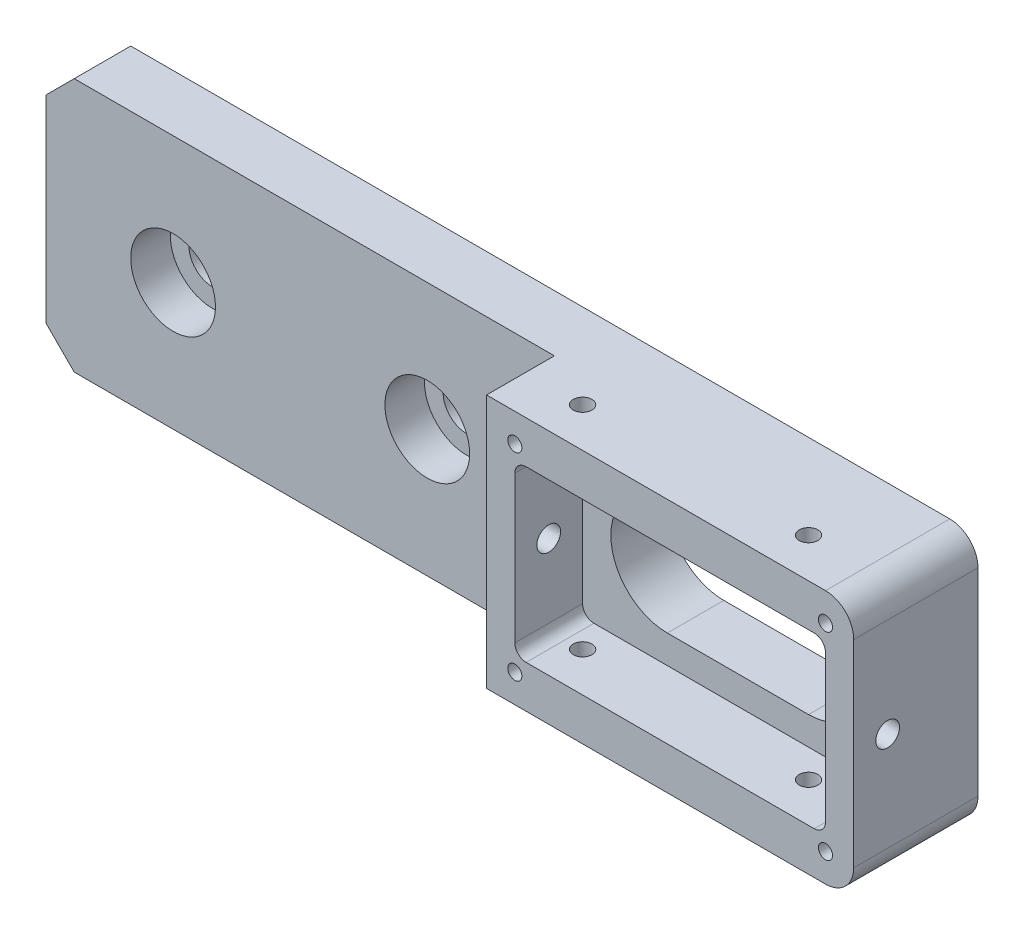
SolidWorks part; units mm, degrees
material "6061 合金"
ref_plane "前视基准面" through (0, 0, 0) normal (0, 0, 1) x (1, 0, 0)
ref_plane "上视基准面" through (0, 0, 0) normal (0, 1, 0) x (1, 0, 0)
ref_plane "右视基准面" through (0, 0, 0) normal (1, 0, 0) x (0, 0, -1)
sketch "Sketch1" plane through (0, 0, 0) normal (0, 0, 1) x (1, 0, 0)
  line L1 (-45.6513, 22.5) -> (109.3487, 22.5)
  line L2 (-45.6513, 22.5) -> (-45.6513, -22.5)
  line L3 (-45.6513, -22.5) -> (109.3487, -22.5)
  line L4 (109.3487, 22.5) -> (109.3487, -22.5)
  dimension "D1" = 45
  dimension "D2" = 155
  dimension "D3" = 22.5
extrude "Boss-Extrude1" add sketch "Sketch1" along normal blind 10
sketch "Sketch2" plane through (0, 0, 10) normal (0, 0, 1) x (1, 0, 0)
  line L0 (-45.6513, -22.5) -> (109.3487, -22.5) construction
  line L1 (109.3487, 22.5) -> (44.3487, 22.5)
  line L2 (109.3487, 22.5) -> (109.3487, -22.5)
  line L3 (109.3487, -22.5) -> (44.3487, -22.5)
  line L4 (44.3487, 22.5) -> (44.3487, -22.5)
  dimension "D1" = 65
extrude "Boss-Extrude2" add sketch "Sketch2" along normal blind 12
sketch "Sketch3" plane through (0, 0, 22) normal (0, 0, 1) x (1, 0, 0)
  line L0 (64.3487, 0) -> (89.3487, 0) construction
  line L1 (64.3487, 10) -> (89.3487, 10)
  line L2 (64.3487, -10) -> (89.3487, -10)
  line L4 (109.3487, -22.5) -> (109.3487, 22.5) construction
  line L5 (44.3487, -22.5) -> (109.3487, -22.5) construction
  arc A0 (64.3487, 10) -> (64.3487, -10) centre (64.3487, 0) ccw
  arc A1 (89.3487, -10) -> (89.3487, 10) centre (89.3487, 0) ccw
  point P2 (76.8487, 0)
  dimension "D4" = 20
  dimension "D1" = 25
  dimension "D2" = 20
  dimension "D3" = 22.5
extrude "Cut-Extrude1" cut sketch "Sketch3" against normal blind 59
sketch "Sketch4" plane through (0, 0, 22) normal (0, 0, 1) x (1, 0, 0)
  line L1 (49.3487, 15) -> (104.3487, 15)
  line L2 (49.3487, 15) -> (49.3487, -15)
  line L3 (49.3487, -15) -> (104.3487, -15)
  line L4 (104.3487, 15) -> (104.3487, -15)
  arc A0 (89.3487, -10) -> (89.3487, 10) centre (89.3487, 0) ccw construction
  arc A1 (64.3487, 10) -> (64.3487, -10) centre (64.3487, 0) ccw construction
  point P4 (99.3487, 0)
  dimension "D1" = 30
  dimension "D2" = 15
  dimension "D3" = 15
  dimension "D4" = 55
extrude "Cut-Extrude2" cut sketch "Sketch4" against normal up to surface (12 mm away) contours L1 L4 L3 L2 up to face at (-0.6513, 5.625, 10)
hole_wizard "M5 Tapped Hole1" positions "Sketch7" profile "Sketch6" tap size "M5" standard "GB" end condition through all
sketch "Sketch7" plane through (44.3487, 0, 0) normal (-1, 0, 0) x (0, 0, 1)
  line L0 (22, 22.5) -> (22, -22.5) construction
  line L1 (0, 0) -> (28.7659, 0) construction
  point P0 (16, 0)
  dimension "D1" = 6
sketch "Sketch6" plane through (44.3487, 0, 16) normal (0, 1, 0) x (0, 0, 1)
  line L0 (0, 0) -> (0, 65)
  line L1 (0, 65) -> (2.1, 65)
  line L2 (2.1, 65) -> (2.1, 0)
  line L5 (2.1, 0) -> (0, 0)
  line L11 (0, -6.35) -> (0, 107.95) construction
  dimension "Thru Tap Drill Dia." = 4.2
  dimension "Thru Tap Drill Depth" = 65
cosmetic thread "Hole Thread1" parameters "D2"=5
hole_wizard "M3 Tapped Hole1" positions "Sketch14" profile "Sketch13" tap size "M3" standard "GB"
sketch "Sketch14" plane through (0, 0, 22) normal (0, 0, 1) x (1, 0, 0)
  line L0 (-45.6513, 0) -> (117.5431, 0) construction
  line L1 (-45.6513, 22.5) -> (-45.6513, -22.5) construction
  line L3 (76.8487, 22.5) -> (76.8487, -27.691) construction
  line L4 (109.3487, 22.5) -> (44.3487, 22.5) construction
  point P0 (104.3487, -17.5)
  point P3 (104.3487, 17.5)
  point P6 (49.3487, -17.5)
  point P9 (49.3487, 17.5)
  dimension "D1" = 35
  dimension "D2" = 55
sketch "Sketch13" plane through (104.3487, -17.5, 22) normal (1, 0, 0) x (0, -1, 0)
  line L0 (0, 0) -> (0, 8.2511)
  line L1 (0, 8.2511) -> (1.25, 7.5)
  line L2 (1.25, 7.5) -> (1.25, 0)
  line L5 (1.25, 0) -> (0, 0)
  line L10 (0, 8.2511) -> (-1.25, 7.5) construction
  line L11 (0, -6.35) -> (0, 107.95) construction
  dimension "Tap Drill Dia." = 2.5
  dimension "Tap Drill Depth" = 7.5
  dimension "Drill Angle" = 118
cosmetic thread "Hole Thread4" parameters "D1"=6, "D2"=3
cosmetic thread "Hole Thread5" parameters "D1"=6, "D2"=3
cosmetic thread "Hole Thread6" parameters "D1"=6, "D2"=3
cosmetic thread "Hole Thread7" parameters "D1"=6, "D2"=3
hole_wizard "M4 螺纹孔1" positions "草图3" profile "草图2" tap size "M4" standard "GB" end condition through all
sketch "草图3" plane through (0, -22.5, 0) normal (0, -1, 0) x (-1, 0, 0)
  line L0 (-109.3487, -15) -> (75.8947, -15) construction
  line L2 (-109.3487, -22) -> (-109.3487, 0) construction
  line L3 (45.6513, 0) -> (-109.3487, 0) construction
  point P0 (-94.3487, -15)
  point P3 (-54.3487, -15)
  dimension "D1" = 40
  dimension "D2" = 15
  dimension "D3" = 15
sketch "草图2" plane through (94.3487, -22.5, 15) normal (1, 0, 0) x (0, 0, -1)
  line L0 (0, 0) -> (0, 45.0001)
  line L1 (0, 45.0001) -> (1.65, 45.0001)
  line L2 (1.65, 45.0001) -> (1.65, 0)
  line L5 (1.65, 0) -> (0, 0)
  line L11 (0, -6.35) -> (0, 107.95) construction
  dimension "通孔螺纹孔钻头直径" = 3.3
  dimension "通孔螺纹孔钻头深度" = 45.0001
cosmetic thread "孔螺蚊线1" parameters "D2"=4
cosmetic thread "孔螺蚊线2" parameters "D2"=4
chamfer "Chamfer1" distance 5 angle 45 2 edges at (-45.6513, -22.5, 5) (-45.6513, 22.5, 5)
fillet "圆角1" radius 5 2 edges at (109.3487, 22.5, 11) (109.3487, -22.5, 11)
fillet "圆角2" radius 2 4 edges at (49.3487, -15, 16) (104.3487, -15, 16) (104.3487, 15, 16) (49.3487, 15, 16)
hole_wizard "打孔尺寸(%根据)内六角圆柱头螺钉的类型1" positions "Sketch17" profile "Sketch16" counterbore size "M8" standard "GB" end condition through all
sketch "Sketch17" plane through (0, 0, 10) normal (0, 0, 1) x (1, 0, 0)
  line L0 (-45.6513, 17.5) -> (-45.6513, -17.5) construction
  line L1 (0, 0) -> (-60.514, 0) construction
  point P0 (21.8487, 0)
  point P3 (-23.1513, 0)
  dimension "D1" = 22.5
  dimension "D2" = 45
sketch "Sketch16" plane through (21.8487, 0, 10) normal (1, 0, 0) x (0, -1, 0)
  line L0 (0, 0) -> (0, 10)
  line L1 (0, 10) -> (4.2, 10)
  line L3 (4.2, 10) -> (4.2, 7)
  line L4 (4.2, 7) -> (7.5, 7)
  line L5 (7.5, 7) -> (7.5, 0)
  line L7 (7.5, 0) -> (0, 0)
  line L11 (0, -6.35) -> (0, 107.95) construction
  dimension "Thru Hole Dia." = 8.4
  dimension "Thru Hole Depth" = 10
  dimension "C'Bore Dia." = 15
  dimension "C'Bore Depth" = 7
